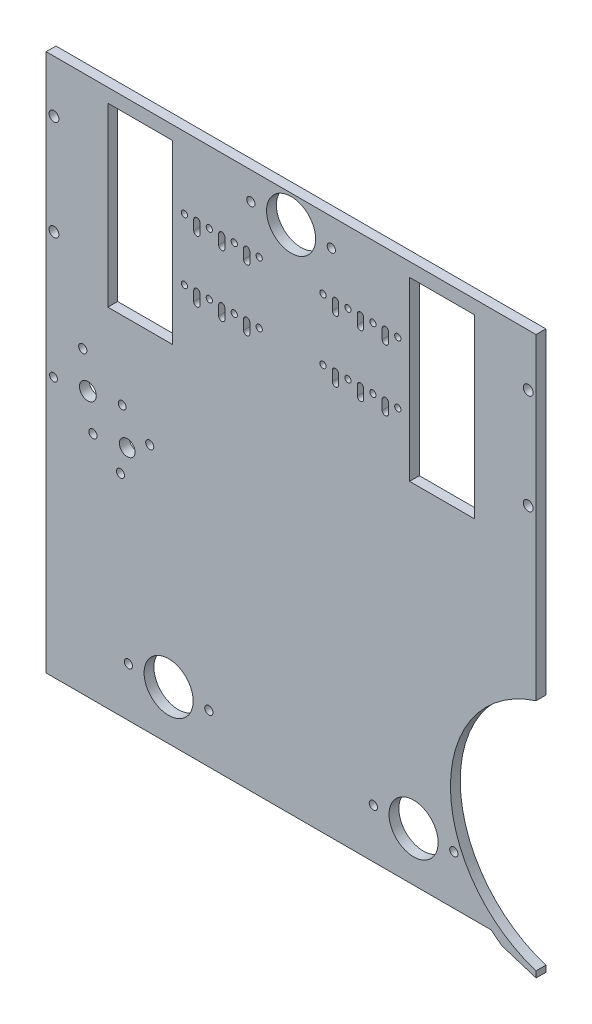
SolidWorks part; units mm, degrees
ref_plane "Front Plane" through (0, 0, 0) normal (0, 0, 1) x (1, 0, 0)
ref_plane "Top Plane" through (0, 0, 0) normal (0, 1, 0) x (1, 0, 0)
ref_plane "Right Plane" through (0, 0, 0) normal (1, 0, 0) x (0, 0, -1)
sketch "Sketch1" plane through (0, 0, 0) normal (0, 0, 1) x (1, 0, 0)
  line L0 (124.8, 0) -> (124.8, -340.9) construction
  line L1 (0, 0) -> (249.6, 0)
  line L2 (0, 0) -> (0, -340.9)
  line L3 (0, -340.9) -> (249.6, -340.9)
  line L4 (249.6, 0) -> (249.6, -340.9)
  line L9 (185.16, -7) -> (218.16, -7)
  line L10 (185.16, -7) -> (185.16, -97)
  line L11 (185.16, -97) -> (218.16, -97)
  line L12 (218.16, -7) -> (218.16, -97)
  line L13 (179.16, -52) -> (228.95, -52) construction
  line L14 (141.06, -36.375) -> (147.41, -36.375) construction
  line L15 (145.3, -14) -> (104.3, -14) construction
  line L21 (179.16, -52) -> (218.16, -52) construction
  line L25 (141.06, -67.625) -> (147.41, -67.625) construction
  line L32 (147.41, -36.375) -> (147.41, -41.375) construction
  line L33 (145.8225, -36.375) -> (145.8225, -41.375)
  line L34 (148.9975, -36.375) -> (148.9975, -41.375)
  line L35 (160.11, -36.375) -> (160.11, -41.375) construction
  line L36 (158.52, -36.375) -> (158.52, -41.375)
  line L37 (161.7, -36.375) -> (161.7, -41.375)
  line L38 (172.81, -36.375) -> (172.81, -41.375) construction
  line L39 (171.22, -36.375) -> (171.22, -41.375)
  line L40 (174.4, -36.375) -> (174.4, -41.375)
  line L41 (147.41, -36.375) -> (153.76, -36.375) construction
  line L42 (153.76, -36.375) -> (160.11, -36.375) construction
  line L43 (160.11, -36.375) -> (166.46, -36.375) construction
  line L44 (166.46, -36.375) -> (172.81, -36.375) construction
  line L45 (172.81, -36.375) -> (179.16, -36.375) construction
  line L48 (228.95, -52) -> (147.41, -52) construction
  line L52 (204.16, -7) -> (204.16, -97) construction
  line L53 (194.16, -7) -> (214.16, -7) construction
  line L54 (194.16, -7) -> (194.16, -97) construction
  line L55 (194.16, -97) -> (214.16, -97) construction
  line L56 (214.16, -7) -> (214.16, -97) construction
  line L62 (147.41, -67.625) -> (147.41, -72.625) construction
  line L65 (145.8225, -67.625) -> (145.8225, -72.625)
  line L68 (148.9975, -67.625) -> (148.9975, -72.625)
  line L71 (160.11, -67.625) -> (160.11, -72.625) construction
  line L78 (158.52, -67.625) -> (158.52, -72.625)
  line L79 (161.7, -67.625) -> (161.7, -72.625)
  line L80 (172.81, -67.625) -> (172.81, -72.625) construction
  line L83 (171.22, -67.625) -> (171.22, -72.625)
  line L87 (147.41, -52) -> (102.19, -52) construction
  line L90 (179.16, -36.375) -> (179.16, -67.625) construction
  line L93 (147.41, -36.375) -> (147.41, -52) construction
  line L102 (245.6, -26.5) -> (245.6, -77.5) construction
  line L103 (218.16, -52) -> (245.6, -52) construction
  line L105 (174.4, -67.625) -> (174.4, -72.625)
  line L106 (147.41, -67.625) -> (153.76, -67.625) construction
  line L107 (153.76, -67.625) -> (160.11, -67.625) construction
  line L108 (160.11, -67.625) -> (166.46, -67.625) construction
  line L109 (166.46, -67.625) -> (172.81, -67.625) construction
  line L110 (172.81, -67.625) -> (179.16, -67.625) construction
  line L111 (102.19, -36.375) -> (102.19, -41.375) construction
  line L112 (103.7775, -36.375) -> (103.7775, -41.375)
  line L113 (100.6025, -36.375) -> (100.6025, -41.375)
  line L114 (89.49, -36.375) -> (89.49, -41.375) construction
  line L115 (91.08, -36.375) -> (91.08, -41.375)
  line L116 (87.9, -36.375) -> (87.9, -41.375)
  line L117 (76.79, -36.375) -> (76.79, -41.375) construction
  line L118 (78.38, -36.375) -> (78.38, -41.375)
  line L119 (75.2, -36.375) -> (75.2, -41.375)
  line L120 (102.19, -67.625) -> (102.19, -72.625) construction
  line L121 (103.7775, -67.625) -> (103.7775, -72.625)
  line L122 (100.6025, -67.625) -> (100.6025, -72.625)
  line L123 (89.49, -67.625) -> (89.49, -72.625) construction
  line L124 (91.08, -67.625) -> (91.08, -72.625)
  line L125 (87.9, -67.625) -> (87.9, -72.625)
  line L126 (76.79, -67.625) -> (76.79, -72.625) construction
  line L127 (78.38, -67.625) -> (78.38, -72.625)
  line L128 (75.2, -67.625) -> (75.2, -72.625)
  line L129 (76.79, -67.625) -> (70.44, -67.625) construction
  line L130 (83.14, -67.625) -> (76.79, -67.625) construction
  line L131 (89.49, -67.625) -> (83.14, -67.625) construction
  line L132 (95.84, -67.625) -> (89.49, -67.625) construction
  line L133 (102.19, -67.625) -> (95.84, -67.625) construction
  line L134 (31.44, -52) -> (4, -52) construction
  line L135 (4, -26.5) -> (4, -77.5) construction
  line L136 (102.19, -36.375) -> (102.19, -52) construction
  line L137 (70.44, -36.375) -> (70.44, -67.625) construction
  line L139 (35.44, -7) -> (35.44, -97) construction
  line L140 (55.44, -97) -> (35.44, -97) construction
  line L141 (55.44, -7) -> (55.44, -97) construction
  line L142 (55.44, -7) -> (35.44, -7) construction
  line L143 (45.44, -7) -> (45.44, -97) construction
  line L144 (20.65, -52) -> (102.19, -52) construction
  line L145 (76.79, -36.375) -> (70.44, -36.375) construction
  line L146 (83.14, -36.375) -> (76.79, -36.375) construction
  line L147 (89.49, -36.375) -> (83.14, -36.375) construction
  line L148 (95.84, -36.375) -> (89.49, -36.375) construction
  line L149 (102.19, -36.375) -> (95.84, -36.375) construction
  line L150 (108.54, -67.625) -> (102.19, -67.625) construction
  line L151 (70.44, -52) -> (31.44, -52) construction
  line L152 (108.54, -36.375) -> (102.19, -36.375) construction
  line L153 (70.44, -52) -> (20.65, -52) construction
  line L154 (31.44, -7) -> (31.44, -97)
  line L155 (64.44, -97) -> (31.44, -97)
  line L156 (64.44, -7) -> (64.44, -97)
  line L157 (64.44, -7) -> (31.44, -7)
  arc A6 (174.4, -36.375) -> (171.22, -36.375) centre (172.81, -36.375) cw construction
  arc A7 (171.22, -36.375) -> (174.4, -36.375) centre (172.81, -36.375) cw
  arc A10 (158.52, -36.375) -> (161.7, -36.375) centre (160.11, -36.375) cw
  arc A11 (161.7, -36.375) -> (158.52, -36.375) centre (160.11, -36.375) cw construction
  arc A14 (145.8225, -36.375) -> (148.9975, -36.375) centre (147.41, -36.375) cw
  arc A15 (148.9975, -36.375) -> (145.8225, -36.375) centre (147.41, -36.375) cw construction
  circle A38 centre (104.3, -14) radius 2.1
  arc A39 (148.9975, -41.375) -> (145.8225, -41.375) centre (147.41, -41.375) cw
  arc A41 (161.7, -41.375) -> (158.52, -41.375) centre (160.11, -41.375) cw
  arc A43 (174.4, -41.375) -> (171.22, -41.375) centre (172.81, -41.375) cw
  circle A84 centre (245.6, -26.5) radius 2.5
  circle A85 centre (245.6, -77.5) radius 2.5
  circle A109 centre (145.3, -14) radius 2.1
  circle A179 centre (179.16, -36.375) radius 1.59
  arc A182 (174.4, -67.625) -> (171.22, -67.625) centre (172.81, -67.625) cw construction
  arc A183 (171.22, -67.625) -> (174.4, -67.625) centre (172.81, -67.625) cw
  arc A184 (158.52, -67.625) -> (161.7, -67.625) centre (160.11, -67.625) cw
  arc A185 (161.7, -67.625) -> (158.52, -67.625) centre (160.11, -67.625) cw construction
  arc A188 (145.8225, -67.625) -> (148.9975, -67.625) centre (147.41, -67.625) cw
  arc A189 (148.9975, -67.625) -> (145.8225, -67.625) centre (147.41, -67.625) cw construction
  arc A193 (148.9975, -72.625) -> (145.8225, -72.625) centre (147.41, -72.625) cw
  arc A195 (161.7, -72.625) -> (158.52, -72.625) centre (160.11, -72.625) cw
  arc A197 (174.4, -72.625) -> (171.22, -72.625) centre (172.81, -72.625) cw
  circle A198 centre (179.16, -67.625) radius 1.59
  circle A199 centre (124.8, -14) radius 12.5
  circle A200 centre (141.06, -36.375) radius 1.59
  circle A201 centre (153.76, -36.375) radius 1.59
  circle A202 centre (166.46, -36.375) radius 1.59
  circle A203 centre (141.06, -67.625) radius 1.59
  circle A204 centre (153.76, -67.625) radius 1.59
  circle A205 centre (166.46, -67.625) radius 1.59
  arc A206 (103.7775, -36.375) -> (100.6025, -36.375) centre (102.19, -36.375) ccw
  arc A207 (100.6025, -41.375) -> (103.7775, -41.375) centre (102.19, -41.375) ccw
  arc A208 (91.08, -36.375) -> (87.9, -36.375) centre (89.49, -36.375) ccw
  arc A209 (87.9, -41.375) -> (91.08, -41.375) centre (89.49, -41.375) ccw
  arc A210 (78.38, -36.375) -> (75.2, -36.375) centre (76.79, -36.375) ccw
  arc A211 (75.2, -41.375) -> (78.38, -41.375) centre (76.79, -41.375) ccw
  arc A212 (103.7775, -67.625) -> (100.6025, -67.625) centre (102.19, -67.625) ccw
  arc A213 (100.6025, -72.625) -> (103.7775, -72.625) centre (102.19, -72.625) ccw
  arc A214 (91.08, -67.625) -> (87.9, -67.625) centre (89.49, -67.625) ccw
  arc A215 (87.9, -72.625) -> (91.08, -72.625) centre (89.49, -72.625) ccw
  arc A216 (78.38, -67.625) -> (75.2, -67.625) centre (76.79, -67.625) ccw
  arc A217 (75.2, -72.625) -> (78.38, -72.625) centre (76.79, -72.625) ccw
  arc A218 (100.6025, -67.625) -> (103.7775, -67.625) centre (102.19, -67.625) ccw construction
  arc A219 (87.9, -67.625) -> (91.08, -67.625) centre (89.49, -67.625) ccw construction
  arc A220 (75.2, -67.625) -> (78.38, -67.625) centre (76.79, -67.625) ccw construction
  arc A221 (100.6025, -36.375) -> (103.7775, -36.375) centre (102.19, -36.375) ccw construction
  arc A222 (87.9, -36.375) -> (91.08, -36.375) centre (89.49, -36.375) ccw construction
  arc A223 (75.2, -36.375) -> (78.38, -36.375) centre (76.79, -36.375) ccw construction
  circle A224 centre (83.14, -67.625) radius 1.59
  circle A225 centre (95.84, -67.625) radius 1.59
  circle A226 centre (108.54, -67.625) radius 1.59
  circle A227 centre (83.14, -36.375) radius 1.59
  circle A228 centre (95.84, -36.375) radius 1.59
  circle A229 centre (108.54, -36.375) radius 1.59
  circle A230 centre (70.44, -67.625) radius 1.59
  circle A234 centre (70.44, -36.375) radius 1.59
  circle A236 centre (4, -77.5) radius 2.5
  circle A237 centre (4, -26.5) radius 2.5
  point P64 (147.41, -52)
  point P65 (102.19, -38.875)
  point P69 (228.95, -52)
  point P71 (221, -87.34)
  point P76 (233.7, -87.34)
  point P78 (221, -54.5)
  point P82 (233.7, -54.5)
  point P86 (246.4, -54.5)
  point P93 (179.16, -52)
  point P97 (246.4, -87.34)
  point P104 (89.49, -38.875)
  point P111 (76.79, -38.875)
  point P119 (102.19, -70.125)
  point P126 (89.49, -70.125)
  point P133 (76.79, -70.125)
  point P155 (124.8, -76.5574)
  point P166 (124.8, -52)
  point P183 (124.8, -76.5574)
  point P199 (70.44, -52)
  point P200 (20.65, -52)
  point P201 (102.19, -52)
  dimension "D5" = 20
  dimension "D10" = 5
  dimension "D12" = 3.18
  dimension "D15" = 5
  dimension "D16" = 5
  dimension "D19" = 3.18
  dimension "D20" = 1.5875
  dimension "D21" = 3.18
  dimension "D22" = 1.59
  dimension "D23" = 3.18
  dimension "D24" = 1.59
  dimension "D25" = 3.18
  dimension "D33" = 3.18
  dimension "D34" = 5
  dimension "D35" = 4.2
  dimension "D32" = 1.5875
  dimension "D36" = 1.59
  dimension "D37" = 3.18
  dimension "D39" = 1.59
  dimension "D47" = 3.18
  dimension "D49" = 25
  dimension "D51" = 4.2
  dimension "D1" = 249.6
  dimension "D2" = 340.9
  dimension "D3" = 4
  dimension "D4" = 90
  dimension "D6" = 90
  dimension "D7" = 9
  dimension "D8" = 6
  dimension "D9" = 5
  dimension "D11" = 6.35
  dimension "D13" = 6.35
  dimension "D14" = 89.36
  dimension "D17" = 25.5
  dimension "D18" = 4
  dimension "D26" = 5
  dimension "D27" = 6.35
  dimension "D28" = 6.35
  dimension "D29" = 6.35
  dimension "D30" = 6.35
  dimension "D31" = 6.35
  dimension "D38" = 7
  dimension "D40" = 5
  dimension "D41" = 6.35
  dimension "D42" = 6.35
  dimension "D43" = 6.35
  dimension "D44" = 6.35
  dimension "D45" = 6.35
  dimension "D46" = 5
  dimension "D48" = 31.25
  dimension "D50" = 20.5
  dimension "14" = 14
extrude "Boss-Extrude1" add sketch "Sketch1" along normal blind 5
sketch "Sketch2" plane through (0, 0, 5) normal (0, 0, 1) x (1, 0, 0)
  line L0 (-27.1214, -80.1211) -> (54.8789, 27.1214) construction
  line L1 (277.1296, -312.7589) -> (359.1299, -205.5164) construction
  line L2 (-27.1214, -80.1211) -> (277.1296, -312.7589) construction
  line L3 (92.2198, 60.8405) -> (87.5714, 58.9986) construction
  line L4 (87.5714, 58.9986) -> (112.9306, -5) construction
  line L5 (120.7692, -11.2093) -> (92.2198, 60.8405) construction
  line L6 (54.8789, 27.1214) -> (359.1299, -205.5164) construction
  line L7 (51.8418, 23.1494) -> (356.0928, -209.4884) construction
  line L8 (-24.0843, -76.1492) -> (280.1666, -308.787) construction
  line L9 (92.2198, 60.8405) -> (96.8682, 62.6824) construction
  line L10 (96.8682, 62.6824) -> (122.2273, -1.3162) construction
  line L11 (178.4848, -231.0386) -> (254.411, -131.74) construction
  line L12 (117.1493, -105.4631) -> (216.4479, -181.3893) construction
  line L13 (79.1862, -155.1124) -> (155.1124, -55.8138) construction
  line L14 (249.6, 0) -> (0, 0) construction
  line L15 (0, 0) -> (0, -340.9) construction
  line L16 (5, -130) -> (130, -130) construction
  line L17 (5, -340.9) -> (5, 0) construction
  line L18 (130, -340.9) -> (130, 0) construction
  line L19 (0, -340.9) -> (0, 0) construction
  line L20 (135, -340.9) -> (135, 0) construction
  line L21 (0, -340.9) -> (33.4202, -340.9) construction
  line L22 (33.4202, -340.9) -> (130, -340.9) construction
  line L23 (130, -340.9) -> (135, -340.9) construction
  line L24 (0, -340.9) -> (249.6, -340.9) construction
  line L25 (0, 0) -> (5, 0) construction
  line L26 (5, 0) -> (130, 0) construction
  line L27 (130, 0) -> (135, 0) construction
  line L28 (249.6, -98.5967) -> (312.6149, -98.5967) construction
  line L29 (249.6, -340.9) -> (249.6, 0) construction
  line L30 (249.6, -158.6746) -> (295.6765, -158.6746) construction
  line L31 (185.16, -97) -> (218.16, -97) construction
  line L32 (194.16, -7.496) -> (194.16, -96.496) construction
  line L33 (180.868, -232.8608) -> (256.7942, -133.5622) construction
  line L34 (249.6, -283.6746) -> (0, -283.6746) construction
  line L35 (0, -5) -> (249.6, -5) construction
  line L36 (249.6, 0) -> (249.6, -5) construction
  line L37 (249.6, -5) -> (249.6, -340.9) construction
  line L38 (249.6, -340.9) -> (5, -340.9) construction
  line L39 (5, -340.9) -> (0, -340.9) construction
  line L40 (0, -335.9) -> (249.6, -335.9) construction
  line L41 (244.6, -340.9) -> (244.6, 0) construction
  circle A0 centre (67.5, -67.5) radius 62.5 construction
  circle A1 centre (268.4804, -221.1746) radius 62.5 construction
  circle A2 centre (67.5, -67.5) radius 67.5 construction
  circle A3 centre (166.7986, -143.4262) radius 62.5 construction
  circle A4 centre (120.7692, -11.2093) radius 77.5 construction
  circle A5 centre (120.7692, -11.2093) radius 2.5 construction
  circle A6 centre (111.5597, 12.0326) radius 1.5 construction
  arc A7 (112.9306, -5) -> (122.2273, -1.3162) centre (120.7692, -11.2093) ccw construction
  point P49 (194.16, -97)
  dimension "D1" = 125
  dimension "D2" = 125
  dimension "D3" = 5
  dimension "D6" = 3
  dimension "D7" = 10
  dimension "D10" = 125
  dimension "D8" = 5
  dimension "D11" = 3
  dimension "D4" = 5
  dimension "D5" = 25
  dimension "D9" = 5
  dimension "D12" = 14
  dimension "D13" = 5
  dimension "D14" = 5
  dimension "D15" = 5
  dimension "D16" = 5
  dimension "D17" = 5
sketch "Sketch4" plane through (0, 0, 5) normal (0, 0, 1) x (1, 0, 0)
  line L3 (249.6, -161.5945) -> (249.6, -280.7546)
  line L5 (249.6, -340.9) -> (249.6, 0) construction
  arc A0 (249.6, -161.5945) -> (249.6, -280.7546) centre (268.4804, -221.1746) ccw
  circle A1 centre (268.4804, -221.1746) radius 62.5 construction
extrude "Cut-Extrude3" cut sketch "Sketch4" along normal blind 193 and the other way blind 193
sketch "Sketch7" plane through (0, 0, 5) normal (0, 0, 1) x (1, 0, 0)
  line L0 (249.6, -283.9016) -> (232.1622, -278.3757)
  line L1 (249.6, -340.9) -> (249.6, -280.7546) construction
  line L2 (232.1622, -278.3757) -> (249.6, -283.9016) construction
  line L3 (-27.1214, -80.1211) -> (277.1296, -312.7589) construction
  line L4 (232.1622, -278.3757) -> (226.6086, -274.1293)
  line L5 (249.6, -283.9016) -> (249.6, -340.9)
  line L6 (249.6, -340.9) -> (0, -340.9)
  line L7 (0, -340.9) -> (0, -274.1293)
  line L10 (0, -340.9) -> (249.6, -340.9) construction
  line L11 (0, 0) -> (0, -340.9) construction
  line L12 (226.6086, -274.1293) -> (0, -274.1293)
extrude "Cut-Extrude6" cut sketch "Sketch7" against normal through all
sketch "Sketch8" plane through (0, 0, 5) normal (0, 0, 1) x (1, 0, 0)
  circle A0 centre (3.765, -141.7184) radius 2
  circle A1 centre (18.6835, -121.6575) radius 2.1
  circle A2 centre (23.8259, -156.6369) radius 2.1
  circle A3 centre (37.8684, -167.0798) radius 2.0586
  circle A4 centre (41.3155, -154.0657) radius 4
  circle A5 centre (38.7444, -136.576) radius 2
  circle A6 centre (21.2547, -139.1472) radius 4.3
  circle A7 centre (52.787, -147.019) radius 2.0586
  circle A8 centre (37.8684, -167.0798) radius 2.0586 construction
  circle A9 centre (52.787, -147.019) radius 2.0586 construction
  circle A10 centre (23.8259, -156.6369) radius 2.1 construction
  circle A11 centre (3.765, -141.7184) radius 2 construction
  circle A12 centre (18.6835, -121.6575) radius 2.1 construction
  circle A13 centre (41.3155, -154.0657) radius 4 construction
  circle A15 centre (21.2547, -139.1472) radius 4.3 construction
  circle A16 centre (38.7444, -136.576) radius 2 construction
extrude "Cut-Extrude7" cut sketch "Sketch8" against normal through all
sketch "Sketch9" plane through (0, 0, 5) normal (0, 0, 1) x (1, 0, 0)
  line L0 (124.8, 0) -> (124.8, -274.1293) construction
  line L1 (249.6, 0) -> (0, 0) construction
  line L2 (226.6086, -274.1293) -> (0, -274.1293) construction
  line L3 (0, -340.9) -> (0, 0) construction
  line L4 (249.6, -161.5945) -> (249.6, 0) construction
  line L5 (62.4, 0) -> (62.4, -274.1293) construction
  line L6 (5, 0) -> (130, 0) construction
  line L7 (41.9, -249.1293) -> (62.4, -249.1293) construction
  line L8 (62.4, -249.1293) -> (82.8847, -249.1293) construction
  line L9 (187.2, -249.1293) -> (166.7153, -249.1293) construction
  line L10 (207.7, -249.1293) -> (187.2, -249.1293) construction
  line L11 (187.2, 0) -> (187.2, -274.1293) construction
  line L12 (203.213, -226.1461) -> (217.7896, -262.8837) construction
  circle A0 centre (62.4, -249.1293) radius 12.5
  circle A2 centre (82.9, -249.1293) radius 2.1
  circle A3 centre (41.9, -249.1293) radius 2.1
  circle A4 centre (207.7, -249.1293) radius 2.1
  circle A5 centre (166.7, -249.1293) radius 2.1
  circle A6 centre (187.2, -249.1293) radius 12.5
  circle A8 centre (268.4804, -221.1746) radius 62.5 construction
  dimension "D1" = 25
  dimension "D2" = 4.2
  dimension "D3" = 4.2
  dimension "D7" = 25
  dimension "D4" = 62.4
  dimension "D5" = 20.5
  dimension "D6" = 20.5
extrude "Cut-Extrude8" cut sketch "Sketch9" against normal through all
